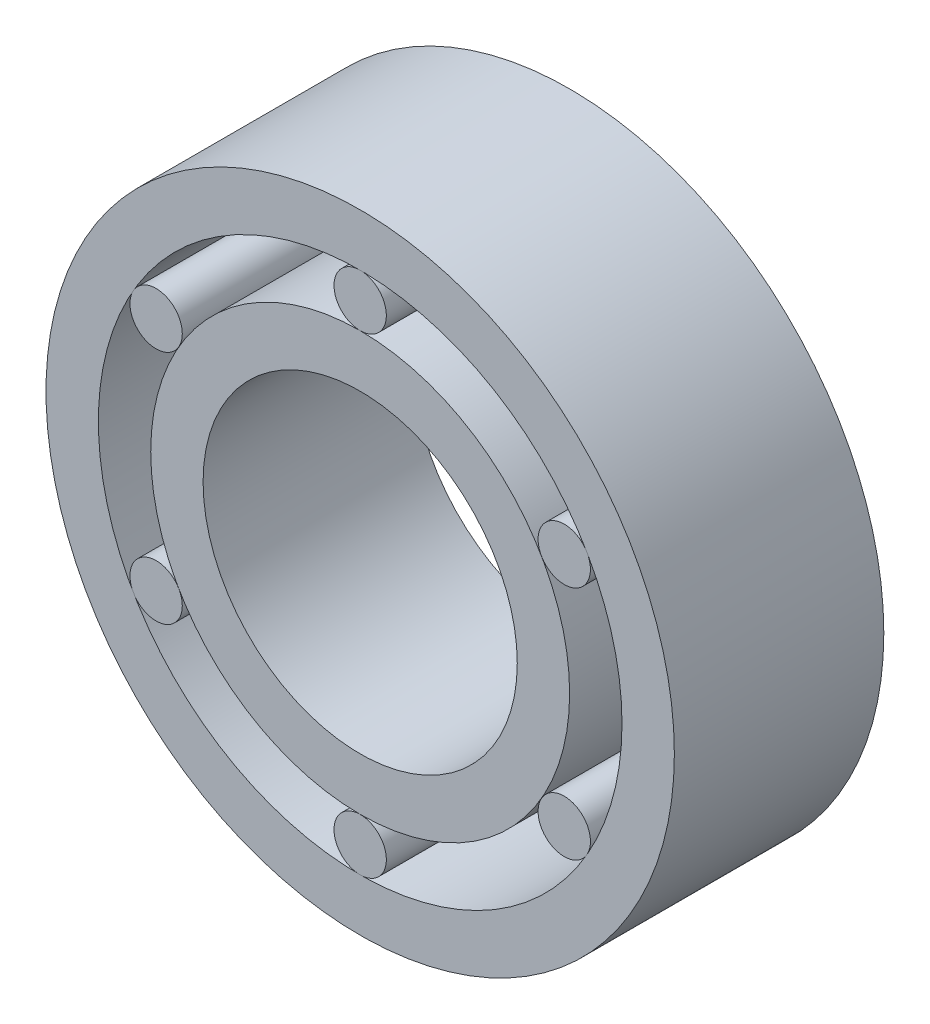
SolidWorks part; units mm, degrees
ref_plane "前视基准面" through (0, 0, 0) normal (0, 0, 1) x (1, 0, 0)
ref_plane "上视基准面" through (0, 0, 0) normal (0, 1, 0) x (1, 0, 0)
ref_plane "右视基准面" through (0, 0, 0) normal (1, 0, 0) x (0, 0, -1)
sketch "草图1" plane through (0, 0, 0) normal (0, 0, 1) x (1, 0, 0)
  circle A0 centre (0, 0) radius 3
  circle A1 centre (0, 0) radius 4
  circle A2 centre (0, 0) radius 6
  circle A3 centre (0, 0) radius 5
  circle A4 centre (0, 4.5) radius 0.5
  circle A5 centre (3.8971, 2.25) radius 0.5
  circle A6 centre (3.8971, -2.25) radius 0.5
  circle A7 centre (0, -4.5) radius 0.5
  circle A8 centre (-3.8971, -2.25) radius 0.5
  circle A9 centre (-3.8971, 2.25) radius 0.5
  point P21 (0, 0)
  dimension "D1" = 6
  dimension "D2" = 8
  dimension "D3" = 12
  dimension "D4" = 10
  dimension "D5" = 6
extrude "凸台-拉伸1" add sketch "草图1" along normal blind 4 contours A1 A0 | A4 | A2 A3 | A9 | A5 | A6 | A7 | A8
